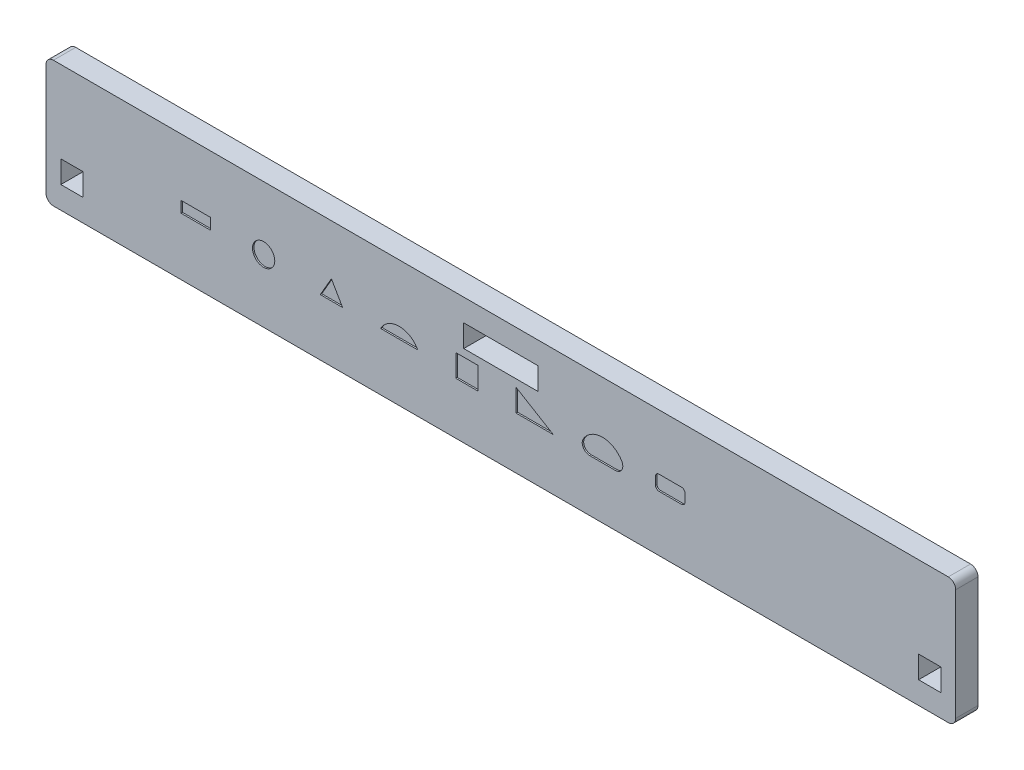
SolidWorks part; units mm, degrees
ref_plane "Спереди" through (0, 0, 0) normal (0, 0, 1) x (1, 0, 0)
ref_plane "Сверху" through (0, 0, 0) normal (0, 1, 0) x (1, 0, 0)
ref_plane "Справа" through (0, 0, 0) normal (1, 0, 0) x (0, 0, -1)
sketch "Эскиз1" plane through (0, 0, 0) normal (0, 0, 1) x (1, 0, 0)
  line L0 (0, 0) -> (0, 24.813) construction
  line L1 (-61.25, 8.5) -> (61.25, 8.5)
  line L2 (-61.25, 8.5) -> (-61.25, -8.5)
  line L3 (-61.25, -8.5) -> (61.25, -8.5)
  line L4 (61.25, 8.5) -> (61.25, -8.5)
  line L5 (-61.25, 8.5) -> (61.25, -8.5) construction
  line L6 (-61.25, -8.5) -> (61.25, 8.5) construction
  line L7 (-5, 5.5) -> (5, 5.5)
  line L8 (-5, 5.5) -> (-5, 2.5)
  line L9 (-5, 2.5) -> (5, 2.5)
  line L10 (5, 5.5) -> (5, 2.5)
  line L11 (-5, 5.5) -> (5, 2.5) construction
  line L12 (-5, 2.5) -> (5, 5.5) construction
  line L13 (56.25, -2.5) -> (59.25, -2.5)
  line L14 (56.25, -2.5) -> (56.25, -5.5)
  line L15 (56.25, -5.5) -> (59.25, -5.5)
  line L16 (59.25, -2.5) -> (59.25, -5.5)
  line L17 (56.25, -2.5) -> (59.25, -5.5) construction
  line L18 (56.25, -5.5) -> (59.25, -2.5) construction
  line L19 (-56.25, -5.5) -> (-59.25, -5.5)
  line L20 (-56.25, -2.5) -> (-56.25, -5.5)
  line L21 (-56.25, -2.5) -> (-59.25, -2.5)
  line L22 (-59.25, -2.5) -> (-59.25, -5.5)
  point P0 (0, 0)
  point P6 (0, 4)
  point P11 (57.75, -4)
  dimension "D1" = 122.5
  dimension "D2" = 115.5
  dimension "D3" = 3
  dimension "D4" = 3
  dimension "D5" = 3
  dimension "D6" = 10
  dimension "D7" = 4.5
  dimension "D8" = 17
  dimension "D9" = 9.5
extrude "Бобышка-Вытянуть1" add sketch "Эскиз1" along normal blind 3
fillet "Скругление1" radius 1 4 edges at (-61.25, 8.5, 1.5) (-61.25, -8.5, 1.5) (61.25, -8.5, 1.5) (61.25, 8.5, 1.5)
sketch "Эскиз2" plane through (0, 0, 3) normal (0, 0, 1) x (1, 0, 0)
  line L5 (-22.8181, 1.7321) -> (-21.3181, -0.866)
  line L6 (-43.07, 0.75) -> (-39.07, 0.75)
  line L10 (-43.07, 0.75) -> (-43.07, -0.75)
  line L15 (-43.07, -0.75) -> (-39.07, -0.75)
  line L16 (-39.07, 0.75) -> (-39.07, -0.75)
  line L17 (-43.07, 0.75) -> (-39.07, -0.75) construction
  line L18 (-43.07, -0.75) -> (-39.07, 0.75) construction
  line L19 (-21.3181, -0.866) -> (-24.3181, -0.866)
  line L20 (-24.3181, -0.866) -> (-22.8181, 1.7321)
  line L21 (-16.1921, -0.75) -> (-11.1921, -0.75)
  line L22 (-24.3181, -0.866) -> (-22.0681, 0.433) construction
  line L23 (-6.0662, -1.5) -> (-3.0662, -1.5)
  line L24 (-6.0662, -1.5) -> (-6.0662, 1.5)
  line L25 (-6.0662, 1.5) -> (-3.0662, 1.5)
  line L26 (-3.0662, -1.5) -> (-3.0662, 1.5)
  line L27 (-22.8181, 1.7321) -> (-22.8181, 0) construction
  line L28 (-13.6921, -0.75) -> (-13.6921, 0.75) construction
  line L29 (-6.0662, -1.5) -> (-3.0662, 1.5) construction
  line L30 (-6.0662, 1.5) -> (-3.0662, -1.5) construction
  line L31 (-41.07, 0) -> (-31.944, 0) construction
  line L32 (-31.944, 0) -> (-22.8181, 0) construction
  line L33 (-22.8181, 0) -> (-13.6921, 0) construction
  line L34 (-13.6921, 0) -> (-4.5662, 0) construction
  line L35 (-59.25, -2.5) -> (-59.25, -5.5) construction
  line L36 (-4.5662, 0) -> (4.5598, 0) construction
  line L37 (4.5598, 0) -> (13.6857, 0) construction
  line L38 (13.6857, 0) -> (22.8117, 0) construction
  line L39 (22.8117, 0) -> (31.9376, 0) construction
  line L40 (31.9376, 0) -> (41.0636, 0) construction
  line L41 (2.0598, -1.5) -> (2.0598, 1.5)
  line L42 (2.0598, 1.5) -> (7.0598, -1.5)
  line L43 (7.0598, -1.5) -> (2.0598, -1.5)
  line L44 (2.0598, -1.5) -> (4.5598, 0) construction
  line L45 (11.9536, -1.5) -> (15.4178, -1.5)
  line L46 (13.6857, -1.5) -> (13.6857, 1.5) construction
  line L48 (21.3117, 1) -> (24.3117, 1)
  line L49 (20.8117, 0.5) -> (20.8117, -0.5)
  line L50 (21.3117, -1) -> (24.3117, -1)
  line L51 (24.8117, 0.5) -> (24.8117, -0.5)
  line L52 (20.8117, 1) -> (24.8117, -1) construction
  line L53 (20.8117, -1) -> (24.8117, 1) construction
  circle A2 centre (-31.944, 0) radius 1.5
  arc A3 (-16.1921, -0.75) -> (-11.1921, -0.75) centre (-13.6921, -2.0833) cw
  arc A4 (11.0876, 0) -> (16.2838, 0) centre (13.6857, -1.5) cw
  arc A5 (11.0876, 0) -> (11.9536, -1.5) centre (11.9536, -0.5) ccw
  arc A6 (16.2838, 0) -> (15.4178, -1.5) centre (15.4178, -0.5) cw
  arc A7 (24.3117, -1) -> (24.8117, -0.5) centre (24.3117, -0.5) ccw
  arc A8 (24.3117, 1) -> (24.8117, 0.5) centre (24.3117, 0.5) cw
  arc A9 (21.3117, 1) -> (20.8117, 0.5) centre (21.3117, 0.5) ccw
  arc A10 (20.8117, -0.5) -> (21.3117, -1) centre (21.3117, -0.5) ccw
  point P1 (-41.07, 0)
  point P21 (-13.6921, -0.75)
  point P25 (-13.6921, 0)
  point P26 (-4.5662, 0)
  point P43 (13.6857, 0)
  point P47 (10.6857, -1.5)
  point P50 (16.6857, -1.5)
  dimension "D3" = 3
  dimension "D12" = 3
  dimension "D13" = 1
  dimension "D16" = 0.5
  dimension "D1" = 3
  dimension "D2" = 1.5
  dimension "D4" = 3
  dimension "D5" = 1.5
  dimension "D6" = 4
  dimension "D7" = 5
  dimension "D8" = 9.126
  dimension "D9" = 18.18
  dimension "D10" = 5
  dimension "D11" = 3
  dimension "D14" = 4
  dimension "D15" = 2
extrude "Вырез-Вытянуть1" cut sketch "Эскиз2" against normal blind 0.2
